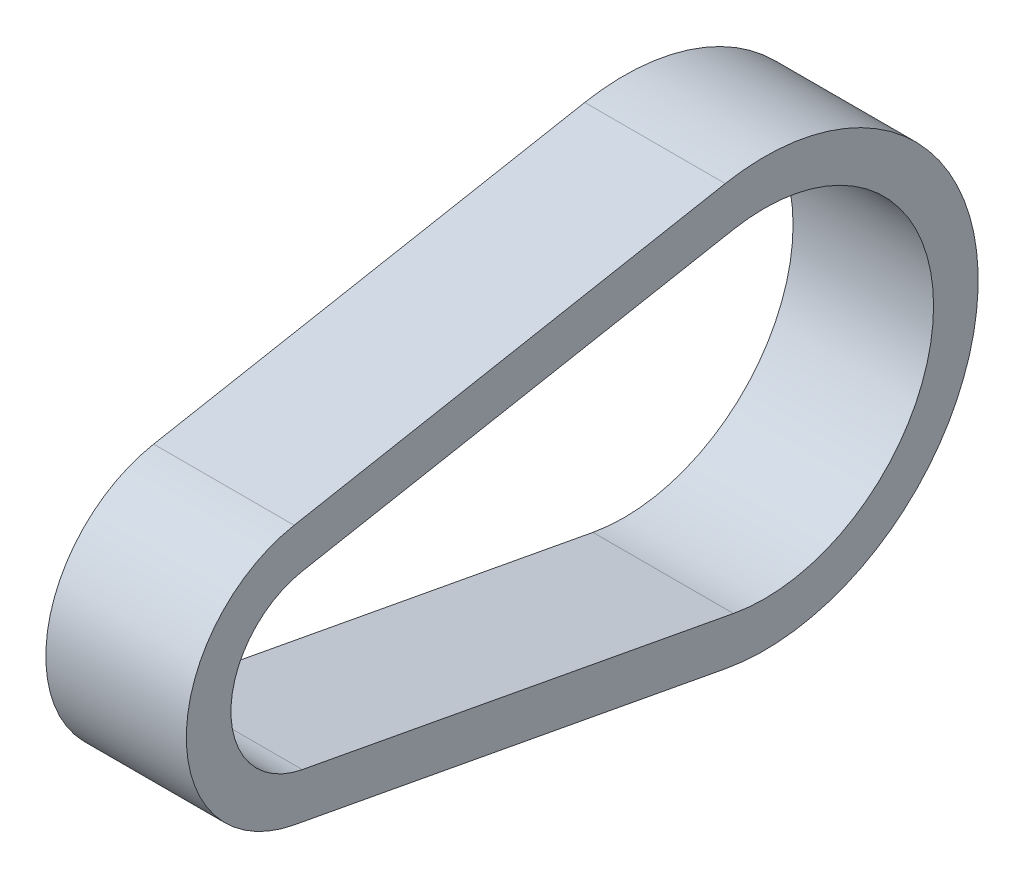
SolidWorks part; units mm, degrees
ref_plane "Front Plane" through (0, 0, 0) normal (0, 0, 1) x (1, 0, 0)
ref_plane "Top Plane" through (0, 0, 0) normal (0, 1, 0) x (1, 0, 0)
ref_plane "Right Plane" through (0, 0, 0) normal (1, 0, 0) x (0, 0, -1)
other "Bounding Box"
ref_plane "Default Plane" through (-8.9266, -12.7485, 0) normal (-0.1736, 0.9848, 0) x (0.9848, 0.1736, 0)
sketch "Sketch1" plane through (0, 0, 0) normal (1, 0, 0) x (0, 0, -1)
  line L0 (0, 0) -> (47.625, 0) construction
  line L1 (-1.7101, 9.1739) -> (44.3156, 17.7536)
  line L2 (-1.7101, -9.1739) -> (44.3156, -17.7536)
  line L3 (-2.5829, 13.8558) -> (43.4428, 22.4354)
  line L4 (-2.5829, -13.8558) -> (43.4428, -22.4354)
  line L5 (-9.332, 0) -> (-14.0945, 0) construction
  line L6 (65.6844, 0) -> (70.4469, 0) construction
  arc A0 (-1.7101, 9.1739) -> (-1.7101, -9.1739) centre (0, 0) ccw
  arc A1 (44.3156, -17.7536) -> (44.3156, 17.7536) centre (47.625, 0) ccw
  arc A2 (-2.5829, 13.8558) -> (-2.5829, -13.8558) centre (0, 0) ccw
  arc A3 (43.4428, -22.4354) -> (43.4428, 22.4354) centre (47.625, 0) ccw
  dimension "D2" = 4.7625
  dimension "D4" = 18.6639
  dimension "D5" = 36.1188
  dimension "D1" = 47.625
extrude "Boss-Extrude1" add sketch "Sketch1" along normal mid plane 15
